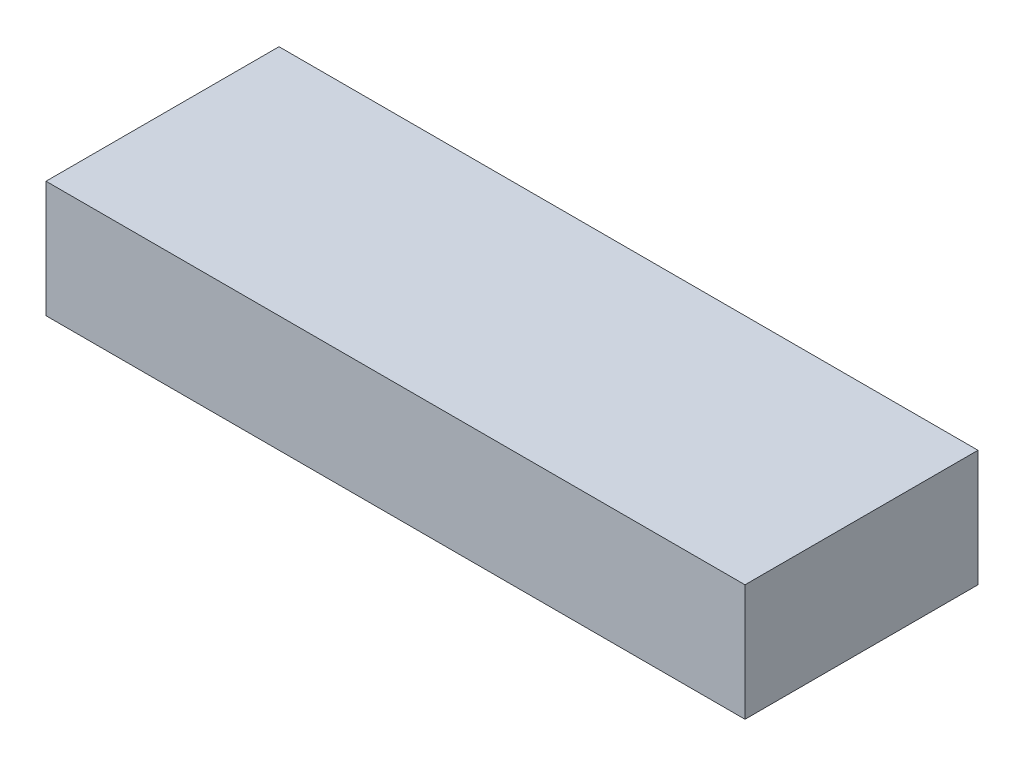
SolidWorks part; units mm, degrees
ref_plane "Front Plane" through (0, 0, 0) normal (0, 0, 1) x (1, 0, 0)
ref_plane "Top Plane" through (0, 0, 0) normal (0, 1, 0) x (1, 0, 0)
ref_plane "Right Plane" through (0, 0, 0) normal (1, 0, 0) x (0, 0, -1)
sketch "Sketch2" plane through (0, 0, 0) normal (0, 1, 0) x (1, 0, 0)
  line L1 (0, 0) -> (152.4, 0)
  line L2 (0, 0) -> (0, 50.8)
  line L3 (0, 50.8) -> (152.4, 50.8)
  line L4 (152.4, 0) -> (152.4, 50.8)
  dimension "D1" = 50.8
  dimension "D2" = 152.4
extrude "Boss-Extrude2" add sketch "Sketch2" along normal blind 25.4
